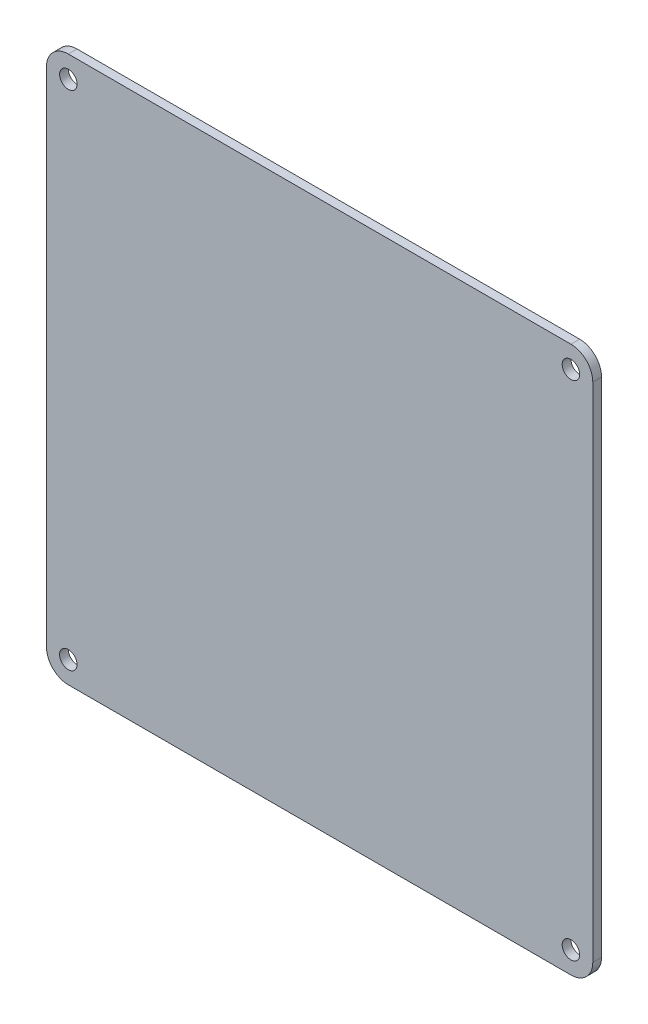
SolidWorks part; units mm, degrees
ref_plane "前视基准面" through (0, 0, 0) normal (0, 0, 1) x (1, 0, 0)
ref_plane "上视基准面" through (0, 0, 0) normal (0, 1, 0) x (1, 0, 0)
ref_plane "右视基准面" through (0, 0, 0) normal (1, 0, 0) x (0, 0, -1)
sketch "草图1" plane through (0, 0, 0) normal (0, 0, 1) x (1, 0, 0)
  line L1 (-46, 50) -> (46, 50)
  line L2 (50, 46) -> (50, -46)
  line L4 (-50, 46) -> (-50, -46)
  line L5 (-46, -50) -> (46, -50)
  line L6 (55, 0) -> (-55, 0) construction
  line L7 (0, -55) -> (0, 55) construction
  circle A0 centre (46, 46) radius 1.6
  arc A1 (50, 46) -> (46, 50) centre (46, 46) ccw
  arc A2 (50, -46) -> (46, -50) centre (46, -46) cw
  circle A3 centre (46, -46) radius 1.6
  arc A4 (-50, -46) -> (-46, -50) centre (-46, -46) ccw
  circle A5 centre (-46, -46) radius 1.6
  circle A6 centre (-46, 46) radius 1.6
  arc A7 (-50, 46) -> (-46, 50) centre (-46, 46) cw
  point P7 (-50, 0)
extrude "凸台-拉伸1" add sketch "草图1" along normal blind 1.6
